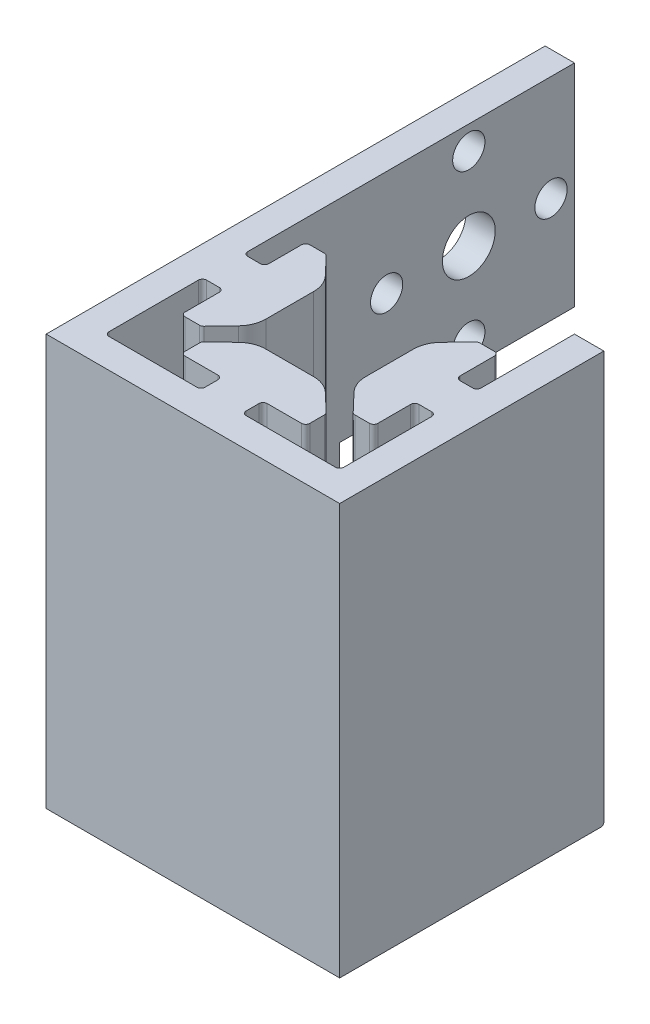
SolidWorks part; units mm, degrees
ref_plane "Front Plane" through (0, 0, 0) normal (0, 0, 1) x (1, 0, 0)
ref_plane "Top Plane" through (0, 0, 0) normal (0, 1, 0) x (1, 0, 0)
ref_plane "Right Plane" through (0, 0, 0) normal (1, 0, 0) x (0, 0, -1)
sketch "Sketch1" plane through (0, 0, 0) normal (0, 1, 0) x (1, 0, 0)
  line L1 (-25, -25) -> (25, -25)
  line L2 (-25, -25) -> (-25, 20)
  line L4 (25, -25) -> (25, 20)
  line L5 (-25, -25) -> (20, 20) construction
  line L6 (-20, 20) -> (25, -25) construction
  line L8 (-20, -20) -> (-20, -3.375)
  line L9 (-20, 20) -> (20, 20)
  line L11 (-20, -20) -> (20, 20) construction
  line L12 (-20, 20) -> (20, -20) construction
  line L13 (-20, 3.625) -> (-16.42, 3.625)
  line L14 (-16.42, 3.625) -> (-16.42, 10.625)
  line L16 (-8.5, 6) -> (-8.5, -6)
  line L18 (-16.42, -10.625) -> (-16.42, -3.375)
  line L19 (-16.42, -3.375) -> (-20, -3.375)
  line L20 (-20, 20) -> (-25, 20)
  line L21 (20, 20) -> (25, 20)
  line L22 (-20, 3.625) -> (-20, 20)
  line L23 (20, -20) -> (3.375, -20)
  line L24 (20, -3.625) -> (20, -20)
  line L25 (-16.42, 10.625) -> (-12.92, 10.625)
  line L26 (-12.92, 10.625) -> (-8.5, 6)
  line L27 (-8.5, -6) -> (-12.92, -10.625)
  line L28 (-12.92, -10.625) -> (-16.42, -10.625)
  line L29 (-3.625, -20) -> (-3.625, -16.42)
  line L30 (-3.625, -16.42) -> (-10.625, -16.42)
  line L31 (-10.625, -16.42) -> (-10.625, -12.92)
  line L32 (-10.625, -12.92) -> (-6, -8.5)
  line L33 (-6, -8.5) -> (6, -8.5)
  line L34 (6, -8.5) -> (10.625, -12.92)
  line L35 (10.625, -12.92) -> (10.625, -16.42)
  line L36 (10.625, -16.42) -> (3.375, -16.42)
  line L37 (3.375, -16.42) -> (3.375, -20)
  line L38 (20, -3.625) -> (16.42, -3.625)
  line L39 (16.42, -3.625) -> (16.42, -10.625)
  line L40 (16.42, -10.625) -> (12.92, -10.625)
  line L41 (12.92, -10.625) -> (8.5, -6)
  line L42 (8.5, -6) -> (8.5, 6)
  line L43 (8.5, 6) -> (12.92, 10.625)
  line L44 (12.92, 10.625) -> (16.42, 10.625)
  line L45 (16.42, 10.625) -> (16.42, 3.375)
  line L46 (16.42, 3.375) -> (20, 3.375)
  line L48 (20, 3.375) -> (20, 20)
  line L50 (-3.625, -20) -> (-20, -20)
  point P0 (0, 0)
  point P5 (0, 0)
  point P21 (-8.5, 0)
  point P47 (0, 0.8)
  point P49 (0, 0)
  dimension "D1" = 50
  dimension "D2" = 3
  dimension "D3" = 5
  dimension "D4" = 7
  dimension "D5" = 11.5
  dimension "D6" = 7.92
  dimension "D7" = 12
  dimension "D8" = 7
  dimension "D9" = 7.25
  dimension "D10" = 3.5
extrude "Boss-Extrude1" add sketch "Sketch1" along normal blind 70
fillet "Fillet4" radius 0.7 26 edges at (-16.42, 35, 3.375) (-16.42, 35, -3.625) (-20, 35, 3.375) (-20, 35, -3.625) (12.92, 35, -10.625) (16.42, 35, -10.625) (16.42, 35, -3.375) (20, 35, -3.375) (12.92, 35, 10.625) (16.42, 35, 10.625) (16.42, 35, 3.625) (20, 35, 3.625) (3.375, 35, 16.42) (3.375, 35, 20) (10.625, 35, 16.42) (10.625, 35, 12.92) (-10.625, 35, 12.92) (-10.625, 35, 16.42) (-3.625, 35, 16.42) (-3.625, 35, 20) (-12.92, 35, 10.625) (-16.42, 35, 10.625) (-12.92, 35, -10.625) (-16.42, 35, -10.625) (-20, 35, 20) (20, 35, 20)
fillet "Fillet6" radius 4.8 6 edges at (-8.5, 35, 6) (-8.5, 35, -6) (6, 35, 8.5) (-6, 35, 8.5) (8.5, 35, 6) (8.5, 35, -6)
ref_plane "Plane2" through (20, 0, -20) normal (1, 0, 0) x (0, 0, -1)
fillet "Fillet12" radius 0.5 1 edges at (22.5, 0, -20)
sketch "Sketch2" plane through (-25, 0, 0) normal (-1, 0, 0) x (0, 0, 1)
  line L0 (-20, 70) -> (-60, 70)
  line L1 (-60, 70) -> (-60, 34)
  line L2 (-60, 34) -> (-20, 34)
  line L3 (-20, 70) -> (-20, 0) construction
  line L8 (-20, 0) -> (25, 0)
  line L9 (25, 0) -> (25, 70)
  line L10 (25, 70) -> (-20, 70)
  line L11 (-20, 70) -> (-20, 0)
  line L15 (-20, 70) -> (-20, 34)
  dimension "D1" = 40
  dimension "D2" = 0
extrude "Boss-Extrude2" add sketch "Sketch2" against normal blind 5
hole_wizard "M5 Clearance Hole1" positions "Sketch6" profile "Sketch4" hole size "M5" standard "ANSI Metric"
sketch "Sketch6" plane through (-25, 0, 0) normal (-1, 0, 0) x (0, 0, 1)
  line L0 (25, 70) -> (-60, 70) construction
  line L1 (-60, 70) -> (-60, 34) construction
  circle A0 centre (-42, 52) radius 14
  point P2 (-56, 52)
  point P25 (-42, 66)
  point P27 (-28, 52)
  point P29 (-42, 38)
  dimension "D1" = 18
  dimension "D2" = 28
  dimension "D3" = 18
  dimension "D4" = 18
sketch "Sketch4" plane through (-25, 52, -56) normal (0, 1, 0) x (0, 0, 1)
  line L0 (0, 0) -> (0, 14.6524)
  line L1 (0, 14.6524) -> (2.75, 13)
  line L2 (2.75, 13) -> (2.75, 0.025)
  line L3 (2.75, 0.025) -> (2.775, 0)
  line L5 (2.775, 0) -> (0, 0)
  line L6 (-2.75, 0.025) -> (-2.775, 0) construction
  line L10 (0, 14.6524) -> (-2.75, 13) construction
  line L11 (0, -6.35) -> (0, 107.95) construction
  dimension "Hole Dia." = 5.5
  dimension "Hole Depth" = 13
  dimension "Near C'Sink Dia." = 5.55
  dimension "Near C'Sink Angle" = 90
  dimension "Drill Angle" = 118
sketch "Sketch7" plane through (-20, 0, 0) normal (1, 0, 0) x (0, 0, -1)
  line L0 (4.325, 70) -> (60, 70) construction
  line L1 (60, 70) -> (60, 34) construction
  circle A0 centre (42, 52) radius 4.5
  dimension "D1" = 18
  dimension "D3" = 9
  dimension "D2" = 18
extrude "Cut-Extrude1" cut sketch "Sketch7" along normal through all both and the other way through all
